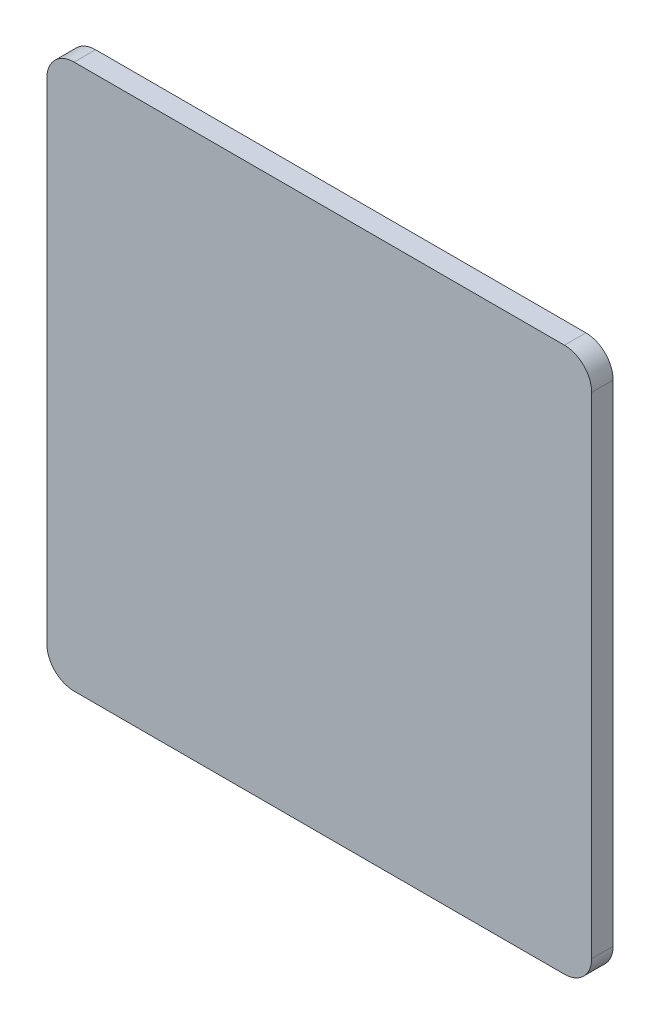
SolidWorks part; units mm, degrees
ref_plane "Front Plane" through (0, 0, 0) normal (0, 0, 1) x (1, 0, 0)
ref_plane "Top Plane" through (0, 0, 0) normal (0, 1, 0) x (1, 0, 0)
ref_plane "Right Plane" through (0, 0, 0) normal (1, 0, 0) x (0, 0, -1)
sketch "Sketch1" plane through (0, 0, 0) normal (0, 0, 1) x (1, 0, 0)
  line L1 (-63.5, -63.5) -> (-63.5, 63.5)
  line L2 (-60.5, -60.5) -> (60.5, -60.5)
  line L3 (-60.5, -60.5) -> (-60.5, 60.5)
  line L4 (-60.5, 60.5) -> (60.5, 60.5)
  line L5 (60.5, -60.5) -> (60.5, 60.5)
  line L6 (-60.5, -60.5) -> (60.5, 60.5) construction
  line L7 (-60.5, 60.5) -> (60.5, -60.5) construction
  line L8 (-63.5, 63.5) -> (63.5, 63.5)
  line L9 (63.5, -63.5) -> (63.5, 63.5)
  line L10 (-63.5, -63.5) -> (63.5, -63.5)
  circle A0 centre (0, 0) radius 44.45 construction
  circle A1 centre (0, 0) radius 38.5
  circle A2 centre (0, 0) radius 60.5 construction
  dimension "D1" = 88.9
  dimension "D2" = 77
  dimension "D3" = 121
  dimension "D4" = 3
extrude "Boss-Extrude1" add sketch "Sketch1" along normal blind 5 contours L1 L10 L9 L8 L5 L2 L3 L4 | L2 L5 L4 L3 A1 | A1
fillet "Fillet1" radius 6.35 4 edges at (63.5, 63.5, 2.5) (63.5, -63.5, 2.5) (-63.5, -63.5, 2.5) (-63.5, 63.5, 2.5)
sketch "Sketch2" plane through (0, 0, 5) normal (0, 0, 1) x (1, 0, 0)
  line L0 (-60.5, 0) -> (60.5, 0) construction
  line L1 (0, -60.5) -> (0, 60.5) construction
  line L2 (53.8, 57.15) -> (53.8, 60.5)
  line L3 (57.15, 53.8) -> (60.5, 53.8)
  line L4 (-53.8, 57.15) -> (-53.8, 60.5)
  line L5 (-57.15, 53.8) -> (-60.5, 53.8)
  line L6 (60.5, 53.8) -> (60.5, -53.8)
  line L7 (57.15, -53.8) -> (60.5, -53.8)
  line L8 (60.5, -57.15) -> (60.5, 57.15)
  line L9 (57.15, 60.5) -> (-57.15, 60.5)
  line L10 (-60.5, 57.15) -> (-60.5, -57.15)
  line L11 (-57.15, -60.5) -> (57.15, -60.5)
  line L13 (53.8, 60.5) -> (-53.8, 60.5)
  line L14 (-60.5, 53.8) -> (-60.5, -53.8)
  line L15 (53.8, -57.15) -> (53.8, -60.5)
  line L16 (-53.8, -57.15) -> (-53.8, -60.5)
  line L17 (-57.15, -53.8) -> (-60.5, -53.8)
  line L18 (53.8, -60.5) -> (-53.8, -60.5)
  circle A0 centre (57.15, 57.15) radius 1.5
  arc A1 (57.15, 53.8) -> (53.8, 57.15) centre (57.15, 57.15) cw
  circle A2 centre (57.15, -57.15) radius 1.5
  arc A3 (57.15, -53.8) -> (53.8, -57.15) centre (57.15, -57.15) ccw
  circle A4 centre (-57.15, 57.15) radius 1.5
  arc A5 (-57.15, 53.8) -> (-53.8, 57.15) centre (-57.15, 57.15) ccw
  circle A6 centre (-57.15, -57.15) radius 1.5
  arc A7 (-57.15, -53.8) -> (-53.8, -57.15) centre (-57.15, -57.15) cw
  arc A8 (60.5, 57.15) -> (57.15, 60.5) centre (57.15, 57.15) ccw
  arc A9 (-57.15, 60.5) -> (-60.5, 57.15) centre (-57.15, 57.15) ccw
  arc A10 (-60.5, -57.15) -> (-57.15, -60.5) centre (-57.15, -57.15) ccw
  arc A11 (57.15, -60.5) -> (60.5, -57.15) centre (57.15, -57.15) ccw
  point P16 (0, 60.5)
  point P23 (-224.2187, 73.6449)
  point P24 (-316.3429, 55.5656)
  point P28 (60.5, 0)
  point P39 (-60.5, 0)
  dimension "D2" = 3
  dimension "D1" = 3
